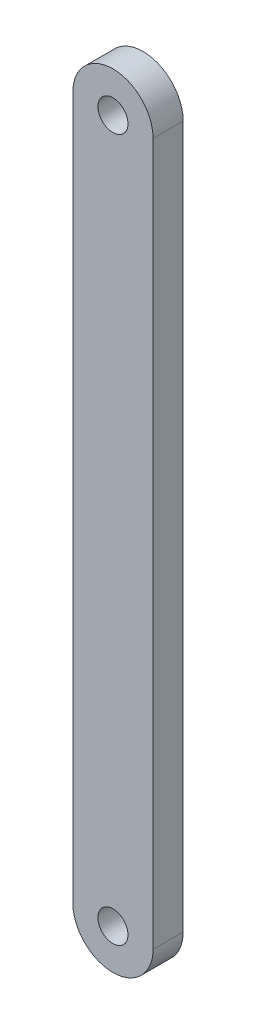
SolidWorks part; units mm, degrees
ref_plane "前视基准面" through (0, 0, 0) normal (0, 0, 1) x (1, 0, 0)
ref_plane "上视基准面" through (0, 0, 0) normal (0, 1, 0) x (1, 0, 0)
ref_plane "右视基准面" through (0, 0, 0) normal (1, 0, 0) x (0, 0, -1)
sketch "草图1" plane through (0, 0, 0) normal (0, 0, 1) x (1, 0, 0)
  line L1 (-4, 35) -> (4, 35)
  line L2 (-4, 35) -> (-4, -35)
  line L3 (-4, -35) -> (4, -35)
  line L4 (4, 35) -> (4, -35)
  line L5 (-4, 35) -> (4, -35) construction
  line L6 (-4, -35) -> (4, 35) construction
  point P0 (0, 0)
  dimension "D1" = 70
  dimension "D2" = 8
extrude "凸台-拉伸1" add sketch "草图1" along normal blind 3
sketch "草图2" plane through (0, 0, 0) normal (0, 0, 1) x (1, 0, 0)
  line L0 (4, 35) -> (-4, 35) construction
  line L1 (-4, -35) -> (4, -35) construction
  circle A0 centre (0, 35) radius 4
  circle A1 centre (0, -35) radius 4
extrude "凸台-拉伸2" add sketch "草图2" along normal blind 3
sketch "草图3" plane through (0, 0, 3) normal (0, 0, 1) x (1, 0, 0)
  circle A0 centre (0, 35) radius 1.5
  circle A1 centre (0, -35) radius 1.5
  dimension "D1" = 3
  dimension "D2" = 3
extrude "切除-拉伸1" cut sketch "草图3" against normal blind 3
